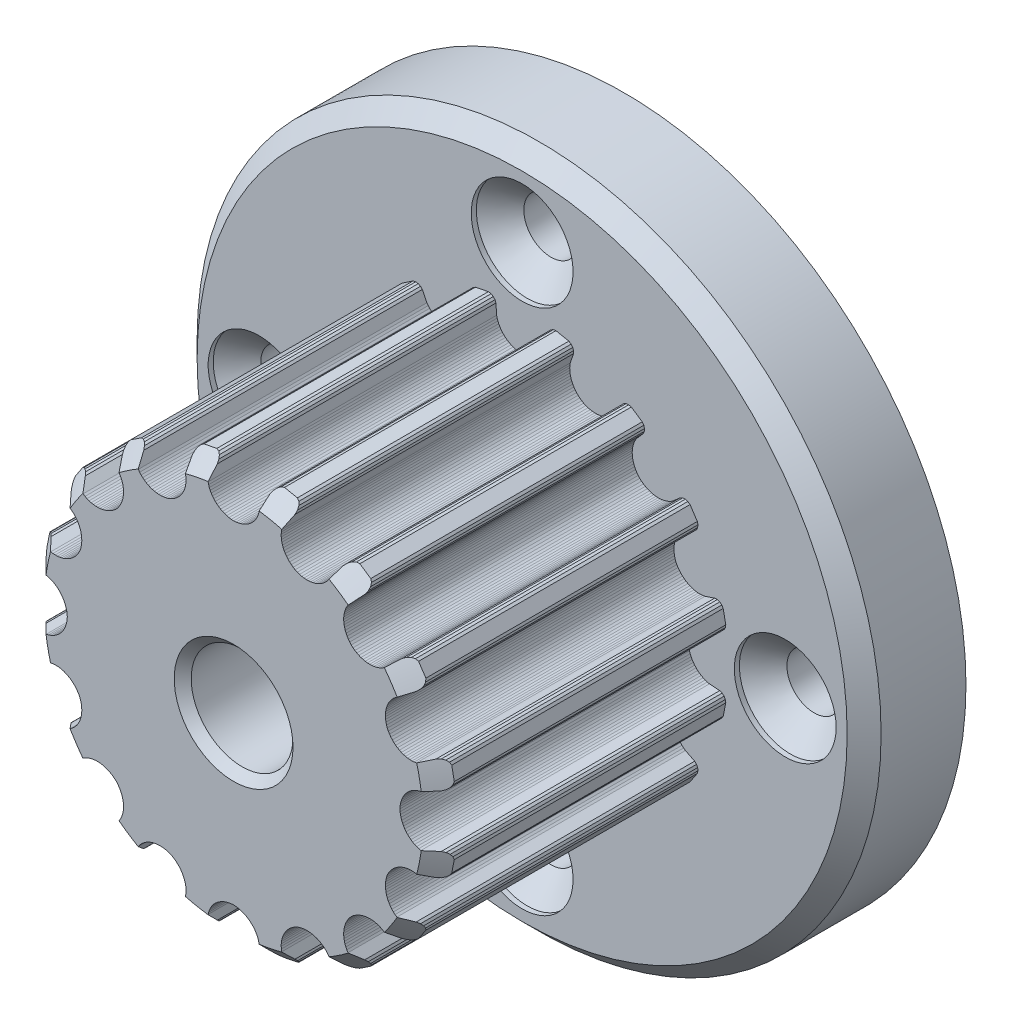
SolidWorks part; units mm, degrees
ref_plane "Front Plane" through (0, 0, 0) normal (0, 0, 1) x (1, 0, 0)
ref_plane "Top Plane" through (0, 0, 0) normal (0, 1, 0) x (1, 0, 0)
ref_plane "Right Plane" through (0, 0, 0) normal (1, 0, 0) x (0, 0, -1)
sketch "Sketch1" plane through (0, 0, 0) normal (0, 0, 1) x (1, 0, 0)
  circle A0 centre (0, 0) radius 15.5
  circle A1 centre (0, 15.5) radius 1.6
  circle A2 centre (15.5, 0) radius 1.6
  circle A3 centre (0, -15.5) radius 1.6
  circle A4 centre (-15.5, 0) radius 1.6
  circle A5 centre (0, 0) radius 20.15
  dimension "D1" = 31
  dimension "D2" = 3.2
  dimension "D3" = 40.3
extrude "Boss-Extrude1" add sketch "Sketch1" along normal blind 6 contours A5 A4 A0 A1 A2 A3 | A4 A0 A3 A2 A1
sketch "Sketch8" plane through (0, 0, 6) normal (0, 0, 1) x (1, 0, 0)
  line L0 (-1.9904, -11.9969) -> (-1.8333, -11.9702)
  line L1 (-1.8333, -11.9702) -> (-1.6992, -11.8961)
  line L2 (-1.6992, -11.8961) -> (-1.5993, -11.7835)
  line L3 (-1.5993, -11.7835) -> (-1.5446, -11.6413)
  line L4 (-1.5446, -11.6413) -> (-1.5027, -11.0359)
  line L5 (-1.5027, -11.0359) -> (-1.4725, -10.9073)
  line L6 (-1.4725, -10.9073) -> (-1.4313, -10.7834)
  line L7 (-1.4313, -10.7834) -> (-1.3796, -10.6646)
  line L8 (-1.3796, -10.6646) -> (-1.3179, -10.5514)
  line L9 (-1.3179, -10.5514) -> (-1.2467, -10.4444)
  line L10 (-1.2467, -10.4444) -> (-1.1667, -10.3438)
  line L11 (-1.1667, -10.3438) -> (-1.0783, -10.2503)
  line L12 (-1.0783, -10.2503) -> (-0.9822, -10.1642)
  line L13 (-0.9822, -10.1642) -> (-0.8789, -10.086)
  line L14 (-0.8789, -10.086) -> (-0.7689, -10.0162)
  line L15 (-0.7689, -10.0162) -> (-0.6528, -9.9552)
  line L16 (-0.6528, -9.9552) -> (-0.5312, -9.9034)
  line L17 (-0.5312, -9.9034) -> (-0.4045, -9.8614)
  line L18 (-0.4045, -9.8614) -> (-0.2734, -9.8296)
  line L19 (-0.2734, -9.8296) -> (-0.1385, -9.8084)
  line L20 (-0.1385, -9.8084) -> (-0.0002, -9.7984)
  line L21 (-0.0002, -9.7984) -> (0.1382, -9.8084)
  line L22 (0.1382, -9.8084) -> (0.2733, -9.8295)
  line L23 (0.2733, -9.8295) -> (0.4045, -9.8613)
  line L24 (0.4045, -9.8613) -> (0.5312, -9.9032)
  line L25 (0.5312, -9.9032) -> (0.6529, -9.9549)
  line L26 (0.6529, -9.9549) -> (0.7691, -10.0159)
  line L27 (0.7691, -10.0159) -> (0.8791, -10.0858)
  line L28 (0.8791, -10.0858) -> (0.9825, -10.1639)
  line L29 (0.9825, -10.1639) -> (1.0786, -10.25)
  line L30 (1.0786, -10.25) -> (1.1669, -10.3436)
  line L31 (1.1669, -10.3436) -> (1.247, -10.4442)
  line L32 (1.247, -10.4442) -> (1.3181, -10.5512)
  line L33 (1.3181, -10.5512) -> (1.3798, -10.6644)
  line L34 (1.3798, -10.6644) -> (1.4315, -10.7832)
  line L35 (1.4315, -10.7832) -> (1.4726, -10.9072)
  line L36 (1.4726, -10.9072) -> (1.5027, -11.0359)
  line L37 (1.5027, -11.0359) -> (1.5446, -11.6413)
  line L38 (1.5446, -11.6413) -> (1.5993, -11.7835)
  line L39 (1.5993, -11.7835) -> (1.6992, -11.8961)
  line L40 (1.6992, -11.8961) -> (1.8333, -11.9702)
  line L41 (1.8333, -11.9702) -> (1.9904, -11.9969)
  line L42 (1.9904, -11.9969) -> (2.7522, -11.8454)
  line L43 (2.7522, -11.8454) -> (2.8871, -11.7606)
  line L44 (2.8871, -11.7606) -> (2.9825, -11.6408)
  line L45 (2.9825, -11.6408) -> (3.0317, -11.4985)
  line L46 (3.0317, -11.4985) -> (3.0279, -11.3462)
  line L47 (3.0279, -11.3462) -> (2.835, -10.7709)
  line L48 (2.835, -10.7709) -> (2.8136, -10.6405)
  line L49 (2.8136, -10.6405) -> (2.8042, -10.5103)
  line L50 (2.8042, -10.5103) -> (2.8066, -10.3807)
  line L51 (2.8066, -10.3807) -> (2.8203, -10.2526)
  line L52 (2.8203, -10.2526) -> (2.8451, -10.1264)
  line L53 (2.8451, -10.1264) -> (2.8805, -10.0029)
  line L54 (2.8805, -10.0029) -> (2.9264, -9.8827)
  line L55 (2.9264, -9.8827) -> (2.9822, -9.7664)
  line L56 (2.9822, -9.7664) -> (3.0478, -9.6546)
  line L57 (3.0478, -9.6546) -> (3.1227, -9.548)
  line L58 (3.1227, -9.548) -> (3.2066, -9.4472)
  line L59 (3.2066, -9.4472) -> (3.2992, -9.3528)
  line L60 (3.2992, -9.3528) -> (3.4001, -9.2656)
  line L61 (3.4001, -9.2656) -> (3.509, -9.186)
  line L62 (3.509, -9.186) -> (3.6256, -9.1148)
  line L63 (3.6256, -9.1148) -> (3.7495, -9.0526)
  line L64 (3.7495, -9.0526) -> (3.8812, -9.0089)
  line L65 (3.8812, -9.0089) -> (4.0141, -8.9767)
  line L66 (4.0141, -8.9767) -> (4.1474, -8.9558)
  line L67 (4.1474, -8.9558) -> (4.2806, -8.9461)
  line L68 (4.2806, -8.9461) -> (4.4128, -8.9473)
  line L69 (4.4128, -8.9473) -> (4.5435, -8.9592)
  line L70 (4.5435, -8.9592) -> (4.6718, -8.9816)
  line L71 (4.6718, -8.9816) -> (4.7972, -9.0143)
  line L72 (4.7972, -9.0143) -> (4.919, -9.057)
  line L73 (4.919, -9.057) -> (5.0364, -9.1097)
  line L74 (5.0364, -9.1097) -> (5.1488, -9.1719)
  line L75 (5.1488, -9.1719) -> (5.2555, -9.2437)
  line L76 (5.2555, -9.2437) -> (5.3558, -9.3246)
  line L77 (5.3558, -9.3246) -> (5.4491, -9.4146)
  line L78 (5.4491, -9.4146) -> (5.5345, -9.5134)
  line L79 (5.5345, -9.5134) -> (5.6115, -9.6208)
  line L80 (5.6115, -9.6208) -> (5.882, -10.164)
  line L81 (5.882, -10.164) -> (5.9869, -10.2745)
  line L82 (5.9869, -10.2745) -> (6.1223, -10.3403)
  line L83 (6.1223, -10.3403) -> (6.2745, -10.3575)
  line L84 (6.2745, -10.3575) -> (6.4299, -10.322)
  line L85 (6.4299, -10.322) -> (7.0757, -9.8905)
  line L86 (7.0757, -9.8905) -> (7.1679, -9.7605)
  line L87 (7.1679, -9.7605) -> (7.2103, -9.6133)
  line L88 (7.2103, -9.6133) -> (7.2013, -9.4631)
  line L89 (7.2013, -9.4631) -> (7.1394, -9.3238)
  line L90 (7.1394, -9.3238) -> (6.741, -8.8661)
  line L91 (6.741, -8.8661) -> (6.6714, -8.7539)
  line L92 (6.6714, -8.7539) -> (6.6129, -8.6371)
  line L93 (6.6129, -8.6371) -> (6.5655, -8.5165)
  line L94 (6.5655, -8.5165) -> (6.5291, -8.3929)
  line L95 (6.5291, -8.3929) -> (6.5037, -8.2669)
  line L96 (6.5037, -8.2669) -> (6.4892, -8.1392)
  line L97 (6.4892, -8.1392) -> (6.4856, -8.0106)
  line L98 (6.4856, -8.0106) -> (6.4926, -7.8817)
  line L99 (6.4926, -7.8817) -> (6.5104, -7.7534)
  line L100 (6.5104, -7.7534) -> (6.5388, -7.6262)
  line L101 (6.5388, -7.6262) -> (6.5778, -7.501)
  line L102 (6.5778, -7.501) -> (6.6272, -7.3784)
  line L103 (6.6272, -7.3784) -> (6.687, -7.2591)
  line L104 (6.687, -7.2591) -> (6.7572, -7.1439)
  line L105 (6.7572, -7.1439) -> (6.8377, -7.0335)
  line L106 (6.8377, -7.0335) -> (6.9284, -6.9286)
  line L107 (6.9284, -6.9286) -> (7.0333, -6.8378)
  line L108 (7.0333, -6.8378) -> (7.1438, -6.7572)
  line L109 (7.1438, -6.7572) -> (7.259, -6.6869)
  line L110 (7.259, -6.6869) -> (7.3783, -6.627)
  line L111 (7.3783, -6.627) -> (7.5009, -6.5775)
  line L112 (7.5009, -6.5775) -> (7.6262, -6.5385)
  line L113 (7.6262, -6.5385) -> (7.7533, -6.5101)
  line L114 (7.7533, -6.5101) -> (7.8817, -6.4923)
  line L115 (7.8817, -6.4923) -> (8.0105, -6.4852)
  line L116 (8.0105, -6.4852) -> (8.1392, -6.4889)
  line L117 (8.1392, -6.4889) -> (8.2669, -6.5034)
  line L118 (8.2669, -6.5034) -> (8.3929, -6.5288)
  line L119 (8.3929, -6.5288) -> (8.5165, -6.5652)
  line L120 (8.5165, -6.5652) -> (8.6371, -6.6127)
  line L121 (8.6371, -6.6127) -> (8.7539, -6.6713)
  line L122 (8.7539, -6.6713) -> (8.8661, -6.741)
  line L123 (8.8661, -6.741) -> (9.3238, -7.1394)
  line L124 (9.3238, -7.1394) -> (9.4631, -7.2013)
  line L125 (9.4631, -7.2013) -> (9.6133, -7.2103)
  line L126 (9.6133, -7.2103) -> (9.7605, -7.1679)
  line L127 (9.7605, -7.1679) -> (9.8905, -7.0757)
  line L128 (9.8905, -7.0757) -> (10.322, -6.4299)
  line L129 (10.322, -6.4299) -> (10.3575, -6.2745)
  line L130 (10.3575, -6.2745) -> (10.3403, -6.1223)
  line L131 (10.3403, -6.1223) -> (10.2745, -5.9869)
  line L132 (10.2745, -5.9869) -> (10.164, -5.882)
  line L133 (10.164, -5.882) -> (9.6208, -5.6115)
  line L134 (9.6208, -5.6115) -> (9.5135, -5.5345)
  line L135 (9.5135, -5.5345) -> (9.4148, -5.449)
  line L136 (9.4148, -5.449) -> (9.3248, -5.3558)
  line L137 (9.3248, -5.3558) -> (9.2439, -5.2554)
  line L138 (9.2439, -5.2554) -> (9.1722, -5.1487)
  line L139 (9.1722, -5.1487) -> (9.11, -5.0363)
  line L140 (9.11, -5.0363) -> (9.0574, -4.9189)
  line L141 (9.0574, -4.9189) -> (9.0146, -4.7971)
  line L142 (9.0146, -4.7971) -> (8.9819, -4.6717)
  line L143 (8.9819, -4.6717) -> (8.9595, -4.5434)
  line L144 (8.9595, -4.5434) -> (8.9476, -4.4128)
  line L145 (8.9476, -4.4128) -> (8.9463, -4.2806)
  line L146 (8.9463, -4.2806) -> (8.956, -4.1475)
  line L147 (8.956, -4.1475) -> (8.9767, -4.0143)
  line L148 (8.9767, -4.0143) -> (9.0088, -3.8815)
  line L149 (9.0088, -3.8815) -> (9.0524, -3.7498)
  line L150 (9.0524, -3.7498) -> (9.1147, -3.6258)
  line L151 (9.1147, -3.6258) -> (9.1859, -3.5091)
  line L152 (9.1859, -3.5091) -> (9.2654, -3.4)
  line L153 (9.2654, -3.4) -> (9.3527, -3.299)
  line L154 (9.3527, -3.299) -> (9.447, -3.2064)
  line L155 (9.447, -3.2064) -> (9.5478, -3.1224)
  line L156 (9.5478, -3.1224) -> (9.6544, -3.0475)
  line L157 (9.6544, -3.0475) -> (9.7662, -2.9819)
  line L158 (9.7662, -2.9819) -> (9.8826, -2.926)
  line L159 (9.8826, -2.926) -> (10.0028, -2.8802)
  line L160 (10.0028, -2.8802) -> (10.1263, -2.8448)
  line L161 (10.1263, -2.8448) -> (10.2525, -2.82)
  line L162 (10.2525, -2.82) -> (10.3807, -2.8064)
  line L163 (10.3807, -2.8064) -> (10.5102, -2.8041)
  line L164 (10.5102, -2.8041) -> (10.6405, -2.8135)
  line L165 (10.6405, -2.8135) -> (10.7709, -2.835)
  line L166 (10.7709, -2.835) -> (11.3462, -3.0279)
  line L167 (11.3462, -3.0279) -> (11.4985, -3.0317)
  line L168 (11.4985, -3.0317) -> (11.6408, -2.9825)
  line L169 (11.6408, -2.9825) -> (11.7606, -2.8871)
  line L170 (11.7606, -2.8871) -> (11.8454, -2.7522)
  line L171 (11.8454, -2.7522) -> (11.9969, -1.9904)
  line L172 (11.9969, -1.9904) -> (11.9702, -1.8333)
  line L173 (11.9702, -1.8333) -> (11.8961, -1.6992)
  line L174 (11.8961, -1.6992) -> (11.7835, -1.5993)
  line L175 (11.7835, -1.5993) -> (11.6413, -1.5446)
  line L176 (11.6413, -1.5446) -> (11.0359, -1.5027)
  line L177 (11.0359, -1.5027) -> (10.9073, -1.4725)
  line L178 (10.9073, -1.4725) -> (10.7834, -1.4313)
  line L179 (10.7834, -1.4313) -> (10.6646, -1.3796)
  line L180 (10.6646, -1.3796) -> (10.5514, -1.3179)
  line L181 (10.5514, -1.3179) -> (10.4444, -1.2467)
  line L182 (10.4444, -1.2467) -> (10.3438, -1.1667)
  line L183 (10.3438, -1.1667) -> (10.2503, -1.0783)
  line L184 (10.2503, -1.0783) -> (10.1642, -0.9822)
  line L185 (10.1642, -0.9822) -> (10.086, -0.8789)
  line L186 (10.086, -0.8789) -> (10.0162, -0.7689)
  line L187 (10.0162, -0.7689) -> (9.9552, -0.6528)
  line L188 (9.9552, -0.6528) -> (9.9034, -0.5312)
  line L189 (9.9034, -0.5312) -> (9.8614, -0.4045)
  line L190 (9.8614, -0.4045) -> (9.8296, -0.2734)
  line L191 (9.8296, -0.2734) -> (9.8084, -0.1385)
  line L192 (9.8084, -0.1385) -> (9.7984, -0.0002)
  line L193 (9.7984, -0.0002) -> (9.8084, 0.1382)
  line L194 (9.8084, 0.1382) -> (9.8295, 0.2733)
  line L195 (9.8295, 0.2733) -> (9.8613, 0.4045)
  line L196 (9.8613, 0.4045) -> (9.9032, 0.5312)
  line L197 (9.9032, 0.5312) -> (9.9549, 0.6529)
  line L198 (9.9549, 0.6529) -> (10.0159, 0.7691)
  line L199 (10.0159, 0.7691) -> (10.0858, 0.8791)
  line L200 (10.0858, 0.8791) -> (10.1639, 0.9825)
  line L201 (10.1639, 0.9825) -> (10.25, 1.0786)
  line L202 (10.25, 1.0786) -> (10.3436, 1.1669)
  line L203 (10.3436, 1.1669) -> (10.4442, 1.247)
  line L204 (10.4442, 1.247) -> (10.5512, 1.3181)
  line L205 (10.5512, 1.3181) -> (10.6644, 1.3798)
  line L206 (10.6644, 1.3798) -> (10.7832, 1.4315)
  line L207 (10.7832, 1.4315) -> (10.9072, 1.4726)
  line L208 (10.9072, 1.4726) -> (11.0359, 1.5027)
  line L209 (11.0359, 1.5027) -> (11.6413, 1.5446)
  line L210 (11.6413, 1.5446) -> (11.7835, 1.5993)
  line L211 (11.7835, 1.5993) -> (11.8961, 1.6992)
  line L212 (11.8961, 1.6992) -> (11.9702, 1.8333)
  line L213 (11.9702, 1.8333) -> (11.9969, 1.9904)
  line L214 (11.9969, 1.9904) -> (11.8454, 2.7522)
  line L215 (11.8454, 2.7522) -> (11.7606, 2.8871)
  line L216 (11.7606, 2.8871) -> (11.6408, 2.9825)
  line L217 (11.6408, 2.9825) -> (11.4985, 3.0317)
  line L218 (11.4985, 3.0317) -> (11.3462, 3.0279)
  line L219 (11.3462, 3.0279) -> (10.7709, 2.835)
  line L220 (10.7709, 2.835) -> (10.6405, 2.8136)
  line L221 (10.6405, 2.8136) -> (10.5103, 2.8042)
  line L222 (10.5103, 2.8042) -> (10.3807, 2.8066)
  line L223 (10.3807, 2.8066) -> (10.2526, 2.8203)
  line L224 (10.2526, 2.8203) -> (10.1264, 2.8451)
  line L225 (10.1264, 2.8451) -> (10.0029, 2.8805)
  line L226 (10.0029, 2.8805) -> (9.8827, 2.9264)
  line L227 (9.8827, 2.9264) -> (9.7664, 2.9822)
  line L228 (9.7664, 2.9822) -> (9.6546, 3.0478)
  line L229 (9.6546, 3.0478) -> (9.548, 3.1227)
  line L230 (9.548, 3.1227) -> (9.4472, 3.2066)
  line L231 (9.4472, 3.2066) -> (9.3528, 3.2992)
  line L232 (9.3528, 3.2992) -> (9.2656, 3.4001)
  line L233 (9.2656, 3.4001) -> (9.186, 3.509)
  line L234 (9.186, 3.509) -> (9.1148, 3.6256)
  line L235 (9.1148, 3.6256) -> (9.0526, 3.7495)
  line L236 (9.0526, 3.7495) -> (9.0089, 3.8812)
  line L237 (9.0089, 3.8812) -> (8.9767, 4.0141)
  line L238 (8.9767, 4.0141) -> (8.9558, 4.1474)
  line L239 (8.9558, 4.1474) -> (8.9461, 4.2806)
  line L240 (8.9461, 4.2806) -> (8.9473, 4.4128)
  line L241 (8.9473, 4.4128) -> (8.9592, 4.5435)
  line L242 (8.9592, 4.5435) -> (8.9816, 4.6718)
  line L243 (8.9816, 4.6718) -> (9.0143, 4.7972)
  line L244 (9.0143, 4.7972) -> (9.057, 4.919)
  line L245 (9.057, 4.919) -> (9.1097, 5.0364)
  line L246 (9.1097, 5.0364) -> (9.1719, 5.1488)
  line L247 (9.1719, 5.1488) -> (9.2437, 5.2555)
  line L248 (9.2437, 5.2555) -> (9.3246, 5.3558)
  line L249 (9.3246, 5.3558) -> (9.4146, 5.4491)
  line L250 (9.4146, 5.4491) -> (9.5134, 5.5345)
  line L251 (9.5134, 5.5345) -> (9.6208, 5.6115)
  line L252 (9.6208, 5.6115) -> (10.164, 5.882)
  line L253 (10.164, 5.882) -> (10.2745, 5.9869)
  line L254 (10.2745, 5.9869) -> (10.3403, 6.1223)
  line L255 (10.3403, 6.1223) -> (10.3575, 6.2745)
  line L256 (10.3575, 6.2745) -> (10.322, 6.4299)
  line L257 (10.322, 6.4299) -> (9.8905, 7.0757)
  line L258 (9.8905, 7.0757) -> (9.7605, 7.1679)
  line L259 (9.7605, 7.1679) -> (9.6133, 7.2103)
  line L260 (9.6133, 7.2103) -> (9.4631, 7.2013)
  line L261 (9.4631, 7.2013) -> (9.3238, 7.1394)
  line L262 (9.3238, 7.1394) -> (8.8661, 6.741)
  line L263 (8.8661, 6.741) -> (8.7539, 6.6714)
  line L264 (8.7539, 6.6714) -> (8.6371, 6.6129)
  line L265 (8.6371, 6.6129) -> (8.5165, 6.5655)
  line L266 (8.5165, 6.5655) -> (8.3929, 6.5291)
  line L267 (8.3929, 6.5291) -> (8.2669, 6.5037)
  line L268 (8.2669, 6.5037) -> (8.1392, 6.4892)
  line L269 (8.1392, 6.4892) -> (8.0106, 6.4856)
  line L270 (8.0106, 6.4856) -> (7.8817, 6.4926)
  line L271 (7.8817, 6.4926) -> (7.7534, 6.5104)
  line L272 (7.7534, 6.5104) -> (7.6262, 6.5388)
  line L273 (7.6262, 6.5388) -> (7.501, 6.5778)
  line L274 (7.501, 6.5778) -> (7.3784, 6.6272)
  line L275 (7.3784, 6.6272) -> (7.2591, 6.687)
  line L276 (7.2591, 6.687) -> (7.1439, 6.7572)
  line L277 (7.1439, 6.7572) -> (7.0335, 6.8377)
  line L278 (7.0335, 6.8377) -> (6.9286, 6.9284)
  line L279 (6.9286, 6.9284) -> (6.8378, 7.0333)
  line L280 (6.8378, 7.0333) -> (6.7572, 7.1438)
  line L281 (6.7572, 7.1438) -> (6.6869, 7.259)
  line L282 (6.6869, 7.259) -> (6.627, 7.3783)
  line L283 (6.627, 7.3783) -> (6.5775, 7.5009)
  line L284 (6.5775, 7.5009) -> (6.5385, 7.6262)
  line L285 (6.5385, 7.6262) -> (6.5101, 7.7533)
  line L286 (6.5101, 7.7533) -> (6.4923, 7.8817)
  line L287 (6.4923, 7.8817) -> (6.4852, 8.0105)
  line L288 (6.4852, 8.0105) -> (6.4889, 8.1392)
  line L289 (6.4889, 8.1392) -> (6.5034, 8.2669)
  line L290 (6.5034, 8.2669) -> (6.5288, 8.3929)
  line L291 (6.5288, 8.3929) -> (6.5652, 8.5165)
  line L292 (6.5652, 8.5165) -> (6.6127, 8.6371)
  line L293 (6.6127, 8.6371) -> (6.6713, 8.7539)
  line L294 (6.6713, 8.7539) -> (6.741, 8.8661)
  line L295 (6.741, 8.8661) -> (7.1394, 9.3238)
  line L296 (7.1394, 9.3238) -> (7.2013, 9.4631)
  line L297 (7.2013, 9.4631) -> (7.2103, 9.6133)
  line L298 (7.2103, 9.6133) -> (7.1679, 9.7605)
  line L299 (7.1679, 9.7605) -> (7.0757, 9.8905)
  line L300 (7.0757, 9.8905) -> (6.4299, 10.322)
  line L301 (6.4299, 10.322) -> (6.2745, 10.3575)
  line L302 (6.2745, 10.3575) -> (6.1223, 10.3403)
  line L303 (6.1223, 10.3403) -> (5.9869, 10.2745)
  line L304 (5.9869, 10.2745) -> (5.882, 10.164)
  line L305 (5.882, 10.164) -> (5.6115, 9.6208)
  line L306 (5.6115, 9.6208) -> (5.5345, 9.5135)
  line L307 (5.5345, 9.5135) -> (5.449, 9.4148)
  line L308 (5.449, 9.4148) -> (5.3558, 9.3248)
  line L309 (5.3558, 9.3248) -> (5.2554, 9.2439)
  line L310 (5.2554, 9.2439) -> (5.1487, 9.1722)
  line L311 (5.1487, 9.1722) -> (5.0363, 9.11)
  line L312 (5.0363, 9.11) -> (4.9189, 9.0574)
  line L313 (4.9189, 9.0574) -> (4.7971, 9.0146)
  line L314 (4.7971, 9.0146) -> (4.6717, 8.9819)
  line L315 (4.6717, 8.9819) -> (4.5434, 8.9595)
  line L316 (4.5434, 8.9595) -> (4.4128, 8.9476)
  line L317 (4.4128, 8.9476) -> (4.2806, 8.9463)
  line L318 (4.2806, 8.9463) -> (4.1475, 8.956)
  line L319 (4.1475, 8.956) -> (4.0143, 8.9767)
  line L320 (4.0143, 8.9767) -> (3.8815, 9.0088)
  line L321 (3.8815, 9.0088) -> (3.7498, 9.0524)
  line L322 (3.7498, 9.0524) -> (3.6258, 9.1147)
  line L323 (3.6258, 9.1147) -> (3.5091, 9.1859)
  line L324 (3.5091, 9.1859) -> (3.4, 9.2654)
  line L325 (3.4, 9.2654) -> (3.299, 9.3527)
  line L326 (3.299, 9.3527) -> (3.2064, 9.447)
  line L327 (3.2064, 9.447) -> (3.1224, 9.5478)
  line L328 (3.1224, 9.5478) -> (3.0475, 9.6544)
  line L329 (3.0475, 9.6544) -> (2.9819, 9.7662)
  line L330 (2.9819, 9.7662) -> (2.926, 9.8826)
  line L331 (2.926, 9.8826) -> (2.8802, 10.0028)
  line L332 (2.8802, 10.0028) -> (2.8448, 10.1263)
  line L333 (2.8448, 10.1263) -> (2.82, 10.2525)
  line L334 (2.82, 10.2525) -> (2.8064, 10.3807)
  line L335 (2.8064, 10.3807) -> (2.8041, 10.5102)
  line L336 (2.8041, 10.5102) -> (2.8135, 10.6405)
  line L337 (2.8135, 10.6405) -> (2.835, 10.7709)
  line L338 (2.835, 10.7709) -> (3.0279, 11.3462)
  line L339 (3.0279, 11.3462) -> (3.0317, 11.4985)
  line L340 (3.0317, 11.4985) -> (2.9825, 11.6408)
  line L341 (2.9825, 11.6408) -> (2.8871, 11.7606)
  line L342 (2.8871, 11.7606) -> (2.7522, 11.8454)
  line L343 (2.7522, 11.8454) -> (1.9904, 11.9969)
  line L344 (1.9904, 11.9969) -> (1.8333, 11.9702)
  line L345 (1.8333, 11.9702) -> (1.6992, 11.8961)
  line L346 (1.6992, 11.8961) -> (1.5993, 11.7835)
  line L347 (1.5993, 11.7835) -> (1.5446, 11.6413)
  line L348 (1.5446, 11.6413) -> (1.5027, 11.0359)
  line L349 (1.5027, 11.0359) -> (1.4725, 10.9073)
  line L350 (1.4725, 10.9073) -> (1.4313, 10.7834)
  line L351 (1.4313, 10.7834) -> (1.3796, 10.6646)
  line L352 (1.3796, 10.6646) -> (1.3179, 10.5514)
  line L353 (1.3179, 10.5514) -> (1.2467, 10.4444)
  line L354 (1.2467, 10.4444) -> (1.1667, 10.3438)
  line L355 (1.1667, 10.3438) -> (1.0783, 10.2503)
  line L356 (1.0783, 10.2503) -> (0.9822, 10.1642)
  line L357 (0.9822, 10.1642) -> (0.8789, 10.086)
  line L358 (0.8789, 10.086) -> (0.7689, 10.0162)
  line L359 (0.7689, 10.0162) -> (0.6528, 9.9552)
  line L360 (0.6528, 9.9552) -> (0.5312, 9.9034)
  line L361 (0.5312, 9.9034) -> (0.4045, 9.8614)
  line L362 (0.4045, 9.8614) -> (0.2734, 9.8296)
  line L363 (0.2734, 9.8296) -> (0.1385, 9.8084)
  line L364 (0.1385, 9.8084) -> (0.0002, 9.7984)
  line L365 (0.0002, 9.7984) -> (-0.1382, 9.8084)
  line L366 (-0.1382, 9.8084) -> (-0.2733, 9.8295)
  line L367 (-0.2733, 9.8295) -> (-0.4045, 9.8613)
  line L368 (-0.4045, 9.8613) -> (-0.5312, 9.9032)
  line L369 (-0.5312, 9.9032) -> (-0.6529, 9.9549)
  line L370 (-0.6529, 9.9549) -> (-0.7691, 10.0159)
  line L371 (-0.7691, 10.0159) -> (-0.8791, 10.0858)
  line L372 (-0.8791, 10.0858) -> (-0.9825, 10.1639)
  line L373 (-0.9825, 10.1639) -> (-1.0786, 10.25)
  line L374 (-1.0786, 10.25) -> (-1.1669, 10.3436)
  line L375 (-1.1669, 10.3436) -> (-1.247, 10.4442)
  line L376 (-1.247, 10.4442) -> (-1.3181, 10.5512)
  line L377 (-1.3181, 10.5512) -> (-1.3798, 10.6644)
  line L378 (-1.3798, 10.6644) -> (-1.4315, 10.7832)
  line L379 (-1.4315, 10.7832) -> (-1.4726, 10.9072)
  line L380 (-1.4726, 10.9072) -> (-1.5027, 11.0359)
  line L381 (-1.5027, 11.0359) -> (-1.5446, 11.6413)
  line L382 (-1.5446, 11.6413) -> (-1.5993, 11.7835)
  line L383 (-1.5993, 11.7835) -> (-1.6992, 11.8961)
  line L384 (-1.6992, 11.8961) -> (-1.8333, 11.9702)
  line L385 (-1.8333, 11.9702) -> (-1.9904, 11.9969)
  line L386 (-1.9904, 11.9969) -> (-2.7522, 11.8454)
  line L387 (-2.7522, 11.8454) -> (-2.8871, 11.7606)
  line L388 (-2.8871, 11.7606) -> (-2.9825, 11.6408)
  line L389 (-2.9825, 11.6408) -> (-3.0317, 11.4985)
  line L390 (-3.0317, 11.4985) -> (-3.0279, 11.3462)
  line L391 (-3.0279, 11.3462) -> (-2.835, 10.7709)
  line L392 (-2.835, 10.7709) -> (-2.8136, 10.6405)
  line L393 (-2.8136, 10.6405) -> (-2.8042, 10.5103)
  line L394 (-2.8042, 10.5103) -> (-2.8066, 10.3807)
  line L395 (-2.8066, 10.3807) -> (-2.8203, 10.2526)
  line L396 (-2.8203, 10.2526) -> (-2.8451, 10.1264)
  line L397 (-2.8451, 10.1264) -> (-2.8805, 10.0029)
  line L398 (-2.8805, 10.0029) -> (-2.9264, 9.8827)
  line L399 (-2.9264, 9.8827) -> (-2.9822, 9.7664)
  line L400 (-2.9822, 9.7664) -> (-3.0478, 9.6546)
  line L401 (-3.0478, 9.6546) -> (-3.1227, 9.548)
  line L402 (-3.1227, 9.548) -> (-3.2066, 9.4472)
  line L403 (-3.2066, 9.4472) -> (-3.2992, 9.3528)
  line L404 (-3.2992, 9.3528) -> (-3.4001, 9.2656)
  line L405 (-3.4001, 9.2656) -> (-3.509, 9.186)
  line L406 (-3.509, 9.186) -> (-3.6256, 9.1148)
  line L407 (-3.6256, 9.1148) -> (-3.7495, 9.0526)
  line L408 (-3.7495, 9.0526) -> (-3.8812, 9.0089)
  line L409 (-3.8812, 9.0089) -> (-4.0141, 8.9767)
  line L410 (-4.0141, 8.9767) -> (-4.1474, 8.9558)
  line L411 (-4.1474, 8.9558) -> (-4.2806, 8.9461)
  line L412 (-4.2806, 8.9461) -> (-4.4128, 8.9473)
  line L413 (-4.4128, 8.9473) -> (-4.5435, 8.9592)
  line L414 (-4.5435, 8.9592) -> (-4.6718, 8.9816)
  line L415 (-4.6718, 8.9816) -> (-4.7972, 9.0143)
  line L416 (-4.7972, 9.0143) -> (-4.919, 9.057)
  line L417 (-4.919, 9.057) -> (-5.0364, 9.1097)
  line L418 (-5.0364, 9.1097) -> (-5.1488, 9.1719)
  line L419 (-5.1488, 9.1719) -> (-5.2555, 9.2437)
  line L420 (-5.2555, 9.2437) -> (-5.3558, 9.3246)
  line L421 (-5.3558, 9.3246) -> (-5.4491, 9.4146)
  line L422 (-5.4491, 9.4146) -> (-5.5345, 9.5134)
  line L423 (-5.5345, 9.5134) -> (-5.6115, 9.6208)
  line L424 (-5.6115, 9.6208) -> (-5.882, 10.164)
  line L425 (-5.882, 10.164) -> (-5.9869, 10.2745)
  line L426 (-5.9869, 10.2745) -> (-6.1223, 10.3403)
  line L427 (-6.1223, 10.3403) -> (-6.2745, 10.3575)
  line L428 (-6.2745, 10.3575) -> (-6.4299, 10.322)
  line L429 (-6.4299, 10.322) -> (-7.0757, 9.8905)
  line L430 (-7.0757, 9.8905) -> (-7.1679, 9.7605)
  line L431 (-7.1679, 9.7605) -> (-7.2103, 9.6133)
  line L432 (-7.2103, 9.6133) -> (-7.2013, 9.4631)
  line L433 (-7.2013, 9.4631) -> (-7.1394, 9.3238)
  line L434 (-7.1394, 9.3238) -> (-6.741, 8.8661)
  line L435 (-6.741, 8.8661) -> (-6.6714, 8.7539)
  line L436 (-6.6714, 8.7539) -> (-6.6129, 8.6371)
  line L437 (-6.6129, 8.6371) -> (-6.5655, 8.5165)
  line L438 (-6.5655, 8.5165) -> (-6.5291, 8.3929)
  line L439 (-6.5291, 8.3929) -> (-6.5037, 8.2669)
  line L440 (-6.5037, 8.2669) -> (-6.4892, 8.1392)
  line L441 (-6.4892, 8.1392) -> (-6.4856, 8.0106)
  line L442 (-6.4856, 8.0106) -> (-6.4926, 7.8817)
  line L443 (-6.4926, 7.8817) -> (-6.5104, 7.7534)
  line L444 (-6.5104, 7.7534) -> (-6.5388, 7.6262)
  line L445 (-6.5388, 7.6262) -> (-6.5778, 7.501)
  line L446 (-6.5778, 7.501) -> (-6.6272, 7.3784)
  line L447 (-6.6272, 7.3784) -> (-6.687, 7.2591)
  line L448 (-6.687, 7.2591) -> (-6.7572, 7.1439)
  line L449 (-6.7572, 7.1439) -> (-6.8377, 7.0335)
  line L450 (-6.8377, 7.0335) -> (-6.9284, 6.9286)
  line L451 (-6.9284, 6.9286) -> (-7.0333, 6.8378)
  line L452 (-7.0333, 6.8378) -> (-7.1438, 6.7572)
  line L453 (-7.1438, 6.7572) -> (-7.259, 6.6869)
  line L454 (-7.259, 6.6869) -> (-7.3783, 6.627)
  line L455 (-7.3783, 6.627) -> (-7.5009, 6.5775)
  line L456 (-7.5009, 6.5775) -> (-7.6262, 6.5385)
  line L457 (-7.6262, 6.5385) -> (-7.7533, 6.5101)
  line L458 (-7.7533, 6.5101) -> (-7.8817, 6.4923)
  line L459 (-7.8817, 6.4923) -> (-8.0105, 6.4852)
  line L460 (-8.0105, 6.4852) -> (-8.1392, 6.4889)
  line L461 (-8.1392, 6.4889) -> (-8.2669, 6.5034)
  line L462 (-8.2669, 6.5034) -> (-8.3929, 6.5288)
  line L463 (-8.3929, 6.5288) -> (-8.5165, 6.5652)
  line L464 (-8.5165, 6.5652) -> (-8.6371, 6.6127)
  line L465 (-8.6371, 6.6127) -> (-8.7539, 6.6713)
  line L466 (-8.7539, 6.6713) -> (-8.8661, 6.741)
  line L467 (-8.8661, 6.741) -> (-9.3238, 7.1394)
  line L468 (-9.3238, 7.1394) -> (-9.4631, 7.2013)
  line L469 (-9.4631, 7.2013) -> (-9.6133, 7.2103)
  line L470 (-9.6133, 7.2103) -> (-9.7605, 7.1679)
  line L471 (-9.7605, 7.1679) -> (-9.8905, 7.0757)
  line L472 (-9.8905, 7.0757) -> (-10.322, 6.4299)
  line L473 (-10.322, 6.4299) -> (-10.3575, 6.2745)
  line L474 (-10.3575, 6.2745) -> (-10.3403, 6.1223)
  line L475 (-10.3403, 6.1223) -> (-10.2745, 5.9869)
  line L476 (-10.2745, 5.9869) -> (-10.164, 5.882)
  line L477 (-10.164, 5.882) -> (-9.6208, 5.6115)
  line L478 (-9.6208, 5.6115) -> (-9.5135, 5.5345)
  line L479 (-9.5135, 5.5345) -> (-9.4148, 5.449)
  line L480 (-9.4148, 5.449) -> (-9.3248, 5.3558)
  line L481 (-9.3248, 5.3558) -> (-9.2439, 5.2554)
  line L482 (-9.2439, 5.2554) -> (-9.1722, 5.1487)
  line L483 (-9.1722, 5.1487) -> (-9.11, 5.0363)
  line L484 (-9.11, 5.0363) -> (-9.0574, 4.9189)
  line L485 (-9.0574, 4.9189) -> (-9.0146, 4.7971)
  line L486 (-9.0146, 4.7971) -> (-8.9819, 4.6717)
  line L487 (-8.9819, 4.6717) -> (-8.9595, 4.5434)
  line L488 (-8.9595, 4.5434) -> (-8.9476, 4.4128)
  line L489 (-8.9476, 4.4128) -> (-8.9463, 4.2806)
  line L490 (-8.9463, 4.2806) -> (-8.956, 4.1475)
  line L491 (-8.956, 4.1475) -> (-8.9767, 4.0143)
  line L492 (-8.9767, 4.0143) -> (-9.0088, 3.8815)
  line L493 (-9.0088, 3.8815) -> (-9.0524, 3.7498)
  line L494 (-9.0524, 3.7498) -> (-9.1147, 3.6258)
  line L495 (-9.1147, 3.6258) -> (-9.1859, 3.5091)
  line L496 (-9.1859, 3.5091) -> (-9.2654, 3.4)
  line L497 (-9.2654, 3.4) -> (-9.3527, 3.299)
  line L498 (-9.3527, 3.299) -> (-9.447, 3.2064)
  line L499 (-9.447, 3.2064) -> (-9.5478, 3.1224)
  line L500 (-9.5478, 3.1224) -> (-9.6544, 3.0475)
  line L501 (-9.6544, 3.0475) -> (-9.7662, 2.9819)
  line L502 (-9.7662, 2.9819) -> (-9.8826, 2.926)
  line L503 (-9.8826, 2.926) -> (-10.0028, 2.8802)
  line L504 (-10.0028, 2.8802) -> (-10.1263, 2.8448)
  line L505 (-10.1263, 2.8448) -> (-10.2525, 2.82)
  line L506 (-10.2525, 2.82) -> (-10.3807, 2.8064)
  line L507 (-10.3807, 2.8064) -> (-10.5102, 2.8041)
  line L508 (-10.5102, 2.8041) -> (-10.6405, 2.8135)
  line L509 (-10.6405, 2.8135) -> (-10.7709, 2.835)
  line L510 (-10.7709, 2.835) -> (-11.3462, 3.0279)
  line L511 (-11.3462, 3.0279) -> (-11.4985, 3.0317)
  line L512 (-11.4985, 3.0317) -> (-11.6408, 2.9825)
  line L513 (-11.6408, 2.9825) -> (-11.7606, 2.8871)
  line L514 (-11.7606, 2.8871) -> (-11.8454, 2.7522)
  line L515 (-11.8454, 2.7522) -> (-11.9969, 1.9904)
  line L516 (-11.9969, 1.9904) -> (-11.9702, 1.8333)
  line L517 (-11.9702, 1.8333) -> (-11.8961, 1.6992)
  line L518 (-11.8961, 1.6992) -> (-11.7835, 1.5993)
  line L519 (-11.7835, 1.5993) -> (-11.6413, 1.5446)
  line L520 (-11.6413, 1.5446) -> (-11.0359, 1.5027)
  line L521 (-11.0359, 1.5027) -> (-10.9073, 1.4725)
  line L522 (-10.9073, 1.4725) -> (-10.7834, 1.4313)
  line L523 (-10.7834, 1.4313) -> (-10.6646, 1.3796)
  line L524 (-10.6646, 1.3796) -> (-10.5514, 1.3179)
  line L525 (-10.5514, 1.3179) -> (-10.4444, 1.2467)
  line L526 (-10.4444, 1.2467) -> (-10.3438, 1.1667)
  line L527 (-10.3438, 1.1667) -> (-10.2503, 1.0783)
  line L528 (-10.2503, 1.0783) -> (-10.1642, 0.9822)
  line L529 (-10.1642, 0.9822) -> (-10.086, 0.8789)
  line L530 (-10.086, 0.8789) -> (-10.0162, 0.7689)
  line L531 (-10.0162, 0.7689) -> (-9.9552, 0.6528)
  line L532 (-9.9552, 0.6528) -> (-9.9034, 0.5312)
  line L533 (-9.9034, 0.5312) -> (-9.8614, 0.4045)
  line L534 (-9.8614, 0.4045) -> (-9.8296, 0.2734)
  line L535 (-9.8296, 0.2734) -> (-9.8084, 0.1385)
  line L536 (-9.8084, 0.1385) -> (-9.7984, 0.0002)
  line L537 (-9.7984, 0.0002) -> (-9.8084, -0.1382)
  line L538 (-9.8084, -0.1382) -> (-9.8295, -0.2733)
  line L539 (-9.8295, -0.2733) -> (-9.8613, -0.4045)
  line L540 (-9.8613, -0.4045) -> (-9.9032, -0.5312)
  line L541 (-9.9032, -0.5312) -> (-9.9549, -0.6529)
  line L542 (-9.9549, -0.6529) -> (-10.0159, -0.7691)
  line L543 (-10.0159, -0.7691) -> (-10.0858, -0.8791)
  line L544 (-10.0858, -0.8791) -> (-10.1639, -0.9825)
  line L545 (-10.1639, -0.9825) -> (-10.25, -1.0786)
  line L546 (-10.25, -1.0786) -> (-10.3436, -1.1669)
  line L547 (-10.3436, -1.1669) -> (-10.4442, -1.247)
  line L548 (-10.4442, -1.247) -> (-10.5512, -1.3181)
  line L549 (-10.5512, -1.3181) -> (-10.6644, -1.3798)
  line L550 (-10.6644, -1.3798) -> (-10.7832, -1.4315)
  line L551 (-10.7832, -1.4315) -> (-10.9072, -1.4726)
  line L552 (-10.9072, -1.4726) -> (-11.0359, -1.5027)
  line L553 (-11.0359, -1.5027) -> (-11.6413, -1.5446)
  line L554 (-11.6413, -1.5446) -> (-11.7835, -1.5993)
  line L555 (-11.7835, -1.5993) -> (-11.8961, -1.6992)
  line L556 (-11.8961, -1.6992) -> (-11.9702, -1.8333)
  line L557 (-11.9702, -1.8333) -> (-11.9969, -1.9904)
  line L558 (-11.9969, -1.9904) -> (-11.8454, -2.7522)
  line L559 (-11.8454, -2.7522) -> (-11.7606, -2.8871)
  line L560 (-11.7606, -2.8871) -> (-11.6408, -2.9825)
  line L561 (-11.6408, -2.9825) -> (-11.4985, -3.0317)
  line L562 (-11.4985, -3.0317) -> (-11.3462, -3.0279)
  line L563 (-11.3462, -3.0279) -> (-10.7709, -2.835)
  line L564 (-10.7709, -2.835) -> (-10.6405, -2.8136)
  line L565 (-10.6405, -2.8136) -> (-10.5103, -2.8042)
  line L566 (-10.5103, -2.8042) -> (-10.3807, -2.8066)
  line L567 (-10.3807, -2.8066) -> (-10.2526, -2.8203)
  line L568 (-10.2526, -2.8203) -> (-10.1264, -2.8451)
  line L569 (-10.1264, -2.8451) -> (-10.0029, -2.8805)
  line L570 (-10.0029, -2.8805) -> (-9.8827, -2.9264)
  line L571 (-9.8827, -2.9264) -> (-9.7664, -2.9822)
  line L572 (-9.7664, -2.9822) -> (-9.6546, -3.0478)
  line L573 (-9.6546, -3.0478) -> (-9.548, -3.1227)
  line L574 (-9.548, -3.1227) -> (-9.4472, -3.2066)
  line L575 (-9.4472, -3.2066) -> (-9.3528, -3.2992)
  line L576 (-9.3528, -3.2992) -> (-9.2656, -3.4001)
  line L577 (-9.2656, -3.4001) -> (-9.186, -3.509)
  line L578 (-9.186, -3.509) -> (-9.1148, -3.6256)
  line L579 (-9.1148, -3.6256) -> (-9.0526, -3.7495)
  line L580 (-9.0526, -3.7495) -> (-9.0089, -3.8812)
  line L581 (-9.0089, -3.8812) -> (-8.9767, -4.0141)
  line L582 (-8.9767, -4.0141) -> (-8.9558, -4.1474)
  line L583 (-8.9558, -4.1474) -> (-8.9461, -4.2806)
  line L584 (-8.9461, -4.2806) -> (-8.9473, -4.4128)
  line L585 (-8.9473, -4.4128) -> (-8.9592, -4.5435)
  line L586 (-8.9592, -4.5435) -> (-8.9816, -4.6718)
  line L587 (-8.9816, -4.6718) -> (-9.0143, -4.7972)
  line L588 (-9.0143, -4.7972) -> (-9.057, -4.919)
  line L589 (-9.057, -4.919) -> (-9.1097, -5.0364)
  line L590 (-9.1097, -5.0364) -> (-9.1719, -5.1488)
  line L591 (-9.1719, -5.1488) -> (-9.2437, -5.2555)
  line L592 (-9.2437, -5.2555) -> (-9.3246, -5.3558)
  line L593 (-9.3246, -5.3558) -> (-9.4146, -5.4491)
  line L594 (-9.4146, -5.4491) -> (-9.5134, -5.5345)
  line L595 (-9.5134, -5.5345) -> (-9.6208, -5.6115)
  line L596 (-9.6208, -5.6115) -> (-10.164, -5.882)
  line L597 (-10.164, -5.882) -> (-10.2745, -5.9869)
  line L598 (-10.2745, -5.9869) -> (-10.3403, -6.1223)
  line L599 (-10.3403, -6.1223) -> (-10.3575, -6.2745)
  line L600 (-10.3575, -6.2745) -> (-10.322, -6.4299)
  line L601 (-10.322, -6.4299) -> (-9.8905, -7.0757)
  line L602 (-9.8905, -7.0757) -> (-9.7605, -7.1679)
  line L603 (-9.7605, -7.1679) -> (-9.6133, -7.2103)
  line L604 (-9.6133, -7.2103) -> (-9.4631, -7.2013)
  line L605 (-9.4631, -7.2013) -> (-9.3238, -7.1394)
  line L606 (-9.3238, -7.1394) -> (-8.8661, -6.741)
  line L607 (-8.8661, -6.741) -> (-8.7539, -6.6714)
  line L608 (-8.7539, -6.6714) -> (-8.6371, -6.6129)
  line L609 (-8.6371, -6.6129) -> (-8.5165, -6.5655)
  line L610 (-8.5165, -6.5655) -> (-8.3929, -6.5291)
  line L611 (-8.3929, -6.5291) -> (-8.2669, -6.5037)
  line L612 (-8.2669, -6.5037) -> (-8.1392, -6.4892)
  line L613 (-8.1392, -6.4892) -> (-8.0106, -6.4856)
  line L614 (-8.0106, -6.4856) -> (-7.8817, -6.4926)
  line L615 (-7.8817, -6.4926) -> (-7.7534, -6.5104)
  line L616 (-7.7534, -6.5104) -> (-7.6262, -6.5388)
  line L617 (-7.6262, -6.5388) -> (-7.501, -6.5778)
  line L618 (-7.501, -6.5778) -> (-7.3784, -6.6272)
  line L619 (-7.3784, -6.6272) -> (-7.2591, -6.687)
  line L620 (-7.2591, -6.687) -> (-7.1439, -6.7572)
  line L621 (-7.1439, -6.7572) -> (-7.0335, -6.8377)
  line L622 (-7.0335, -6.8377) -> (-6.9286, -6.9284)
  line L623 (-6.9286, -6.9284) -> (-6.8378, -7.0333)
  line L624 (-6.8378, -7.0333) -> (-6.7572, -7.1438)
  line L625 (-6.7572, -7.1438) -> (-6.6869, -7.259)
  line L626 (-6.6869, -7.259) -> (-6.627, -7.3783)
  line L627 (-6.627, -7.3783) -> (-6.5775, -7.5009)
  line L628 (-6.5775, -7.5009) -> (-6.5385, -7.6262)
  line L629 (-6.5385, -7.6262) -> (-6.5101, -7.7533)
  line L630 (-6.5101, -7.7533) -> (-6.4923, -7.8817)
  line L631 (-6.4923, -7.8817) -> (-6.4852, -8.0105)
  line L632 (-6.4852, -8.0105) -> (-6.4889, -8.1392)
  line L633 (-6.4889, -8.1392) -> (-6.5034, -8.2669)
  line L634 (-6.5034, -8.2669) -> (-6.5288, -8.3929)
  line L635 (-6.5288, -8.3929) -> (-6.5652, -8.5165)
  line L636 (-6.5652, -8.5165) -> (-6.6127, -8.6371)
  line L637 (-6.6127, -8.6371) -> (-6.6713, -8.7539)
  line L638 (-6.6713, -8.7539) -> (-6.741, -8.8661)
  line L639 (-6.741, -8.8661) -> (-7.1394, -9.3238)
  line L640 (-7.1394, -9.3238) -> (-7.2013, -9.4631)
  line L641 (-7.2013, -9.4631) -> (-7.2103, -9.6133)
  line L642 (-7.2103, -9.6133) -> (-7.1679, -9.7605)
  line L643 (-7.1679, -9.7605) -> (-7.0757, -9.8905)
  line L644 (-7.0757, -9.8905) -> (-6.4299, -10.322)
  line L645 (-6.4299, -10.322) -> (-6.2745, -10.3575)
  line L646 (-6.2745, -10.3575) -> (-6.1223, -10.3403)
  line L647 (-6.1223, -10.3403) -> (-5.9869, -10.2745)
  line L648 (-5.9869, -10.2745) -> (-5.882, -10.164)
  line L649 (-5.882, -10.164) -> (-5.6115, -9.6208)
  line L650 (-5.6115, -9.6208) -> (-5.5345, -9.5135)
  line L651 (-5.5345, -9.5135) -> (-5.449, -9.4148)
  line L652 (-5.449, -9.4148) -> (-5.3558, -9.3248)
  line L653 (-5.3558, -9.3248) -> (-5.2554, -9.2439)
  line L654 (-5.2554, -9.2439) -> (-5.1487, -9.1722)
  line L655 (-5.1487, -9.1722) -> (-5.0363, -9.11)
  line L656 (-5.0363, -9.11) -> (-4.9189, -9.0574)
  line L657 (-4.9189, -9.0574) -> (-4.7971, -9.0146)
  line L658 (-4.7971, -9.0146) -> (-4.6717, -8.9819)
  line L659 (-4.6717, -8.9819) -> (-4.5434, -8.9595)
  line L660 (-4.5434, -8.9595) -> (-4.4128, -8.9476)
  line L661 (-4.4128, -8.9476) -> (-4.2806, -8.9463)
  line L662 (-4.2806, -8.9463) -> (-4.1475, -8.956)
  line L663 (-4.1475, -8.956) -> (-4.0143, -8.9767)
  line L664 (-4.0143, -8.9767) -> (-3.8815, -9.0088)
  line L665 (-3.8815, -9.0088) -> (-3.7498, -9.0524)
  line L666 (-3.7498, -9.0524) -> (-3.6258, -9.1147)
  line L667 (-3.6258, -9.1147) -> (-3.5091, -9.1859)
  line L668 (-3.5091, -9.1859) -> (-3.4, -9.2654)
  line L669 (-3.4, -9.2654) -> (-3.299, -9.3527)
  line L670 (-3.299, -9.3527) -> (-3.2064, -9.447)
  line L671 (-3.2064, -9.447) -> (-3.1224, -9.5478)
  line L672 (-3.1224, -9.5478) -> (-3.0475, -9.6544)
  line L673 (-3.0475, -9.6544) -> (-2.9819, -9.7662)
  line L674 (-2.9819, -9.7662) -> (-2.926, -9.8826)
  line L675 (-2.926, -9.8826) -> (-2.8802, -10.0028)
  line L676 (-2.8802, -10.0028) -> (-2.8448, -10.1263)
  line L677 (-2.8448, -10.1263) -> (-2.82, -10.2525)
  line L678 (-2.82, -10.2525) -> (-2.8064, -10.3807)
  line L679 (-2.8064, -10.3807) -> (-2.8041, -10.5102)
  line L680 (-2.8041, -10.5102) -> (-2.8135, -10.6405)
  line L681 (-2.8135, -10.6405) -> (-2.835, -10.7709)
  line L682 (-2.835, -10.7709) -> (-3.0279, -11.3462)
  line L683 (-3.0279, -11.3462) -> (-3.0317, -11.4985)
  line L684 (-3.0317, -11.4985) -> (-2.9825, -11.6408)
  line L685 (-2.9825, -11.6408) -> (-2.8871, -11.7606)
  line L686 (-2.8871, -11.7606) -> (-2.7522, -11.8454)
  line L687 (-2.7522, -11.8454) -> (-1.9904, -11.9969)
extrude "Boss-Extrude3" add sketch "Sketch8" along normal blind 17
sketch "Sketch9" plane through (0, 0, 0) normal (0, 0, -1) x (-1, 0, 0)
  circle A0 centre (0, 0) radius 1.5
  dimension "D1" = 3
extrude "Cut-Extrude1" cut sketch "Sketch9" against normal blind 6.25
hole_wizard "CSK for M3 Flat Head Machine Screw1" positions "Sketch10" profile "Sketch12" countersink size "M3" standard "ANSI Metric" end condition up to next
sketch "Sketch10" plane through (0, 0, 6) normal (0, 0, 1) x (1, 0, 0)
  point P0 (0, 15.5)
  point P3 (15.5, 0)
  point P6 (0, -15.5)
  point P9 (-15.5, 0)
sketch "Sketch12" plane through (0, 15.5, 6) normal (1, 0, 0) x (0, -1, 0)
  line L0 (0, 0) -> (0, 6)
  line L1 (0, 6) -> (1.5, 6)
  line L2 (1.5, 6) -> (1.5, 1.8)
  line L3 (1.5, 1.8) -> (3, 0.3)
  line L4 (3, 0.3) -> (3, 0)
  line L6 (3, 0) -> (0, 0)
  line L7 (-1.5, 1.8) -> (-3, 0.3) construction
  line L11 (0, -6.35) -> (0, 107.95) construction
  dimension "Thru Hole Dia." = 3
  dimension "Thru Hole Depth" = 6
  dimension "C'Sink Dia." = 6
  dimension "C'Sink Angle" = 90
  dimension "Head Clearance" = 0.3
chamfer "Chamfer1" distance 1 angle 45 1 edges at (20.15, 0, 6)
ref_axis "Axis1" through (0, 0, 31.6588) along (0, 0, -1)
ref_plane "Plane5" through (0, 0, 0) normal (0.1951, 0.9808, 0) x (0.9808, -0.1951, 0)
sketch "Sketch13" plane through (0, 0, 0) normal (0.1951, 0.9808, 0) x (0, 0, -1)
  line L4 (-23, 12.6547) -> (-23, 11.1547)
  line L5 (-23, 11.1547) -> (-21.5, 12.6547)
  line L7 (-21.5, 12.6547) -> (-23, 12.6547)
  line L8 (-23, 12.1547) -> (-6, 12.1547) construction
  dimension "D1" = 1.5
  dimension "D2" = 0.5
revolve "Cut-Revolve4" cut sketch "Sketch13" angle 360 about axis through (0, 0, 31.6588) along (0, 0, -1)
sketch "Sketch14" plane through (0, 0, 23) normal (0, 0, 1) x (1, 0, 0)
  circle A0 centre (0, 0) radius 3
  dimension "D1" = 6
extrude "Cut-Extrude2" cut sketch "Sketch14" against normal blind 17
chamfer "Chamfer2" distance 0.5 angle 45 1 edges at (3, 0, 23)
equation "\"D3@Sketch1\"=20.15*2"
equation "\"TEETH\"= 16"
equation "\"PITCH\"= 5mm"
equation "\"C\"= \"TEETH\" * \"PITCH\""
equation "\"RADIUS\"= \"C\" / ( 2 * PI )"
